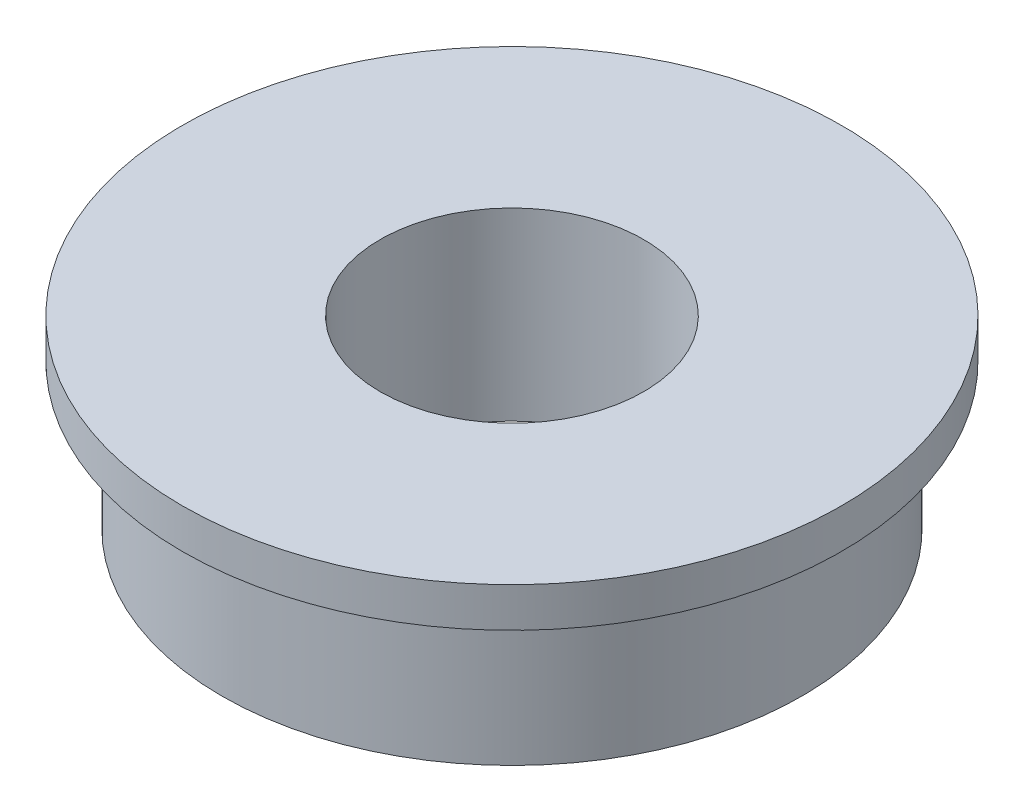
SolidWorks part; units mm, degrees
material "Cast Alloy Steel"
ref_plane "Front Plane" through (0, 0, 0) normal (0, 0, 1) x (1, 0, 0)
ref_plane "Top Plane" through (0, 0, 0) normal (0, 1, 0) x (1, 0, 0)
ref_plane "Right Plane" through (0, 0, 0) normal (1, 0, 0) x (0, 0, -1)
sketch "Sketch1" plane through (0, 0, 0) normal (0, 1, 0) x (1, 0, 0)
  circle A0 centre (0, 0) radius 11
  circle A1 centre (0, 0) radius 5
  dimension "D1" = 22
  dimension "D2" = 10
extrude "Boss-Extrude1" add sketch "Sketch1" along normal mid plane 7
sketch "Sketch2" plane through (0, 3.5, 0) normal (0, 1, 0) x (1, 0, 0)
  circle A0 centre (0, 0) radius 12.5
  circle A1 centre (0, 0) radius 11 construction
  circle A2 centre (0, 0) radius 11
  dimension "D1" = 25
extrude "Boss-Extrude2" add sketch "Sketch2" against normal blind 1.5
